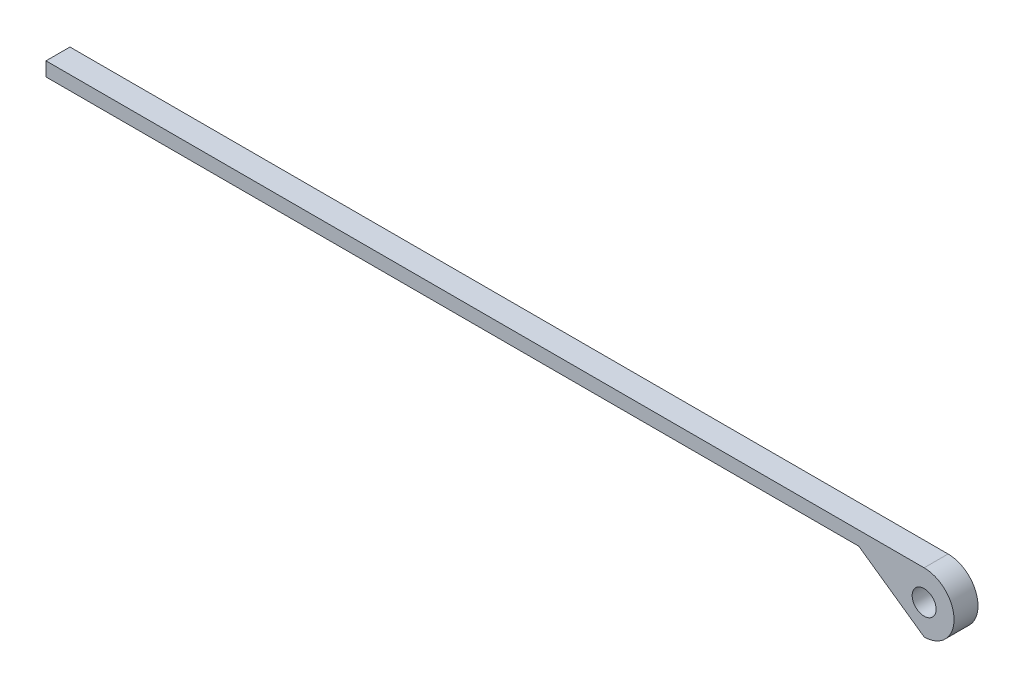
SolidWorks part; units mm, degrees
material "ABS"
ref_plane "Front Plane" through (0, 0, 0) normal (0, 0, 1) x (1, 0, 0)
ref_plane "Top Plane" through (0, 0, 0) normal (0, 1, 0) x (1, 0, 0)
ref_plane "Right Plane" through (0, 0, 0) normal (1, 0, 0) x (0, 0, -1)
sketch "Sketch1" plane through (0, 0, 0) normal (0, 0, 1) x (1, 0, 0)
  line L0 (210, 399.8061) -> (-10, 399.8061)
  line L1 (-10, 399.8061) -> (-10, 396.3061)
  line L2 (-10, 396.3061) -> (193.6369, 396.3061)
  line L3 (193.6369, 396.3061) -> (210, 384.8061)
  circle A1 centre (210, 392.3061) radius 3 construction
  circle A3 centre (210, 392.3061) radius 3
  arc A4 (210, 384.8061) -> (210, 399.8061) centre (210, 392.3061) ccw
  dimension "D1" = 15
  dimension "D2" = 220
  dimension "D3" = 3.5
  dimension "D4" = 20
extrude "Boss-Extrude1" add sketch "Sketch1" along normal blind 6
